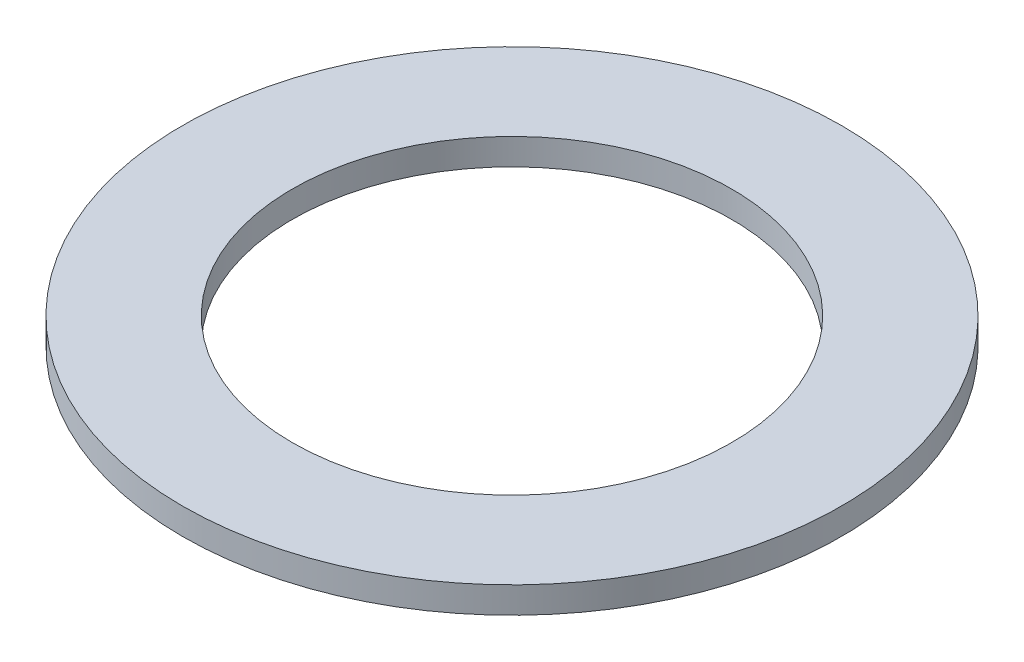
SolidWorks part; units mm, degrees
ref_plane "Front Plane" through (0, 0, 0) normal (0, 0, 1) x (1, 0, 0)
ref_plane "Top Plane" through (0, 0, 0) normal (0, 1, 0) x (1, 0, 0)
ref_plane "Right Plane" through (0, 0, 0) normal (1, 0, 0) x (0, 0, -1)
sketch "Sketch1" plane through (0, 0, 0) normal (0, 1, 0) x (1, 0, 0)
  circle A0 centre (0, 0) radius 9.525
  dimension "OD" = 19.05
extrude "Boss-Extrude1" add sketch "Sketch1" along normal blind 0.762
sketch "Sketch5" plane through (0, 0.762, 0) normal (0, 1, 0) x (-1, 0, 0)
  circle A0 centre (0, 0) radius 6.35
  dimension "ID" = 12.7
extrude "Cut-Extrude1" cut sketch "Sketch5" against normal through all
